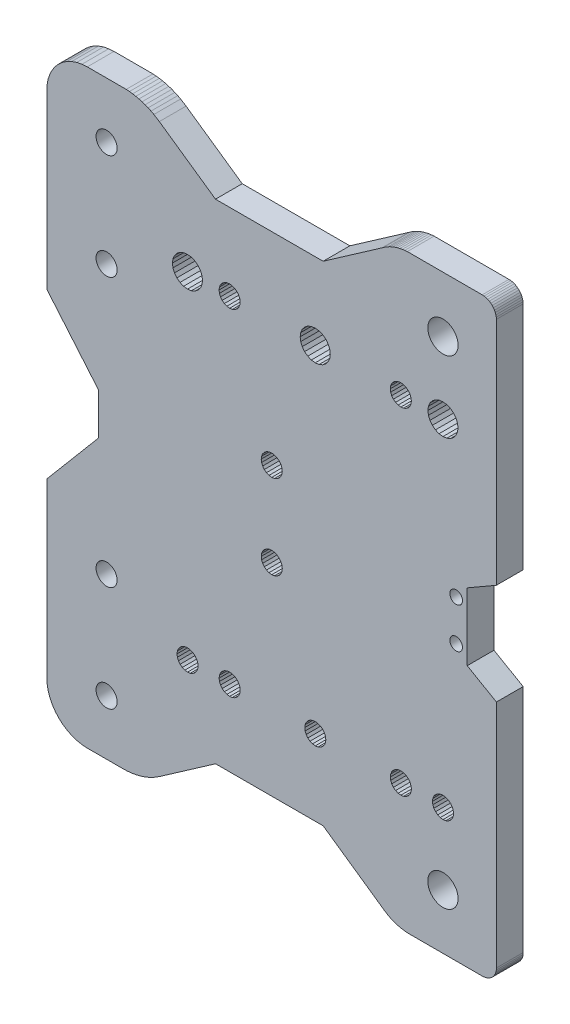
SolidWorks part; units mm, degrees
ref_plane "Front Plane" through (0, 0, 0) normal (0, 0, 1) x (1, 0, 0)
ref_plane "Top Plane" through (0, 0, 0) normal (0, 1, 0) x (1, 0, 0)
ref_plane "Right Plane" through (0, 0, 0) normal (1, 0, 0) x (0, 0, -1)
sketch "Model" plane through (0, 0, 0) normal (0, 0, 1) x (1, 0, 0)
  line L0 (606.5044, 163.4555) -> (606.5078, 147.4555)
  line L1 (516.3162, 225.4614) -> (516.3365, 85.4197) construction
  line L2 (516.3264, 155.4406) -> (606.5061, 155.4555) construction
  line L3 (600.743, 195.2513) -> (600.743, 115.4517) construction
  line L4 (606.5078, 147.4555) -> (613.436, 143.4555)
  line L5 (613.4326, 167.4555) -> (606.5044, 163.4555)
  line L8 (606.5078, 151.9787) -> (606.5068, 151.9792)
  line L12 (547.9387, 193.9942) -> (548.336, 193.4765)
  line L13 (557.9459, 144.2266) -> (558.3432, 143.7089)
  line L14 (598.5902, 114.201) -> (598.9876, 113.6833)
  line L15 (597.6529, 197.0356) -> (597.2965, 196.1749)
  line L16 (537.9502, 114.1922) -> (538.3476, 113.6745)
  line L17 (547.9502, 114.2067) -> (548.3476, 113.689)
  line L18 (567.3374, 197.0312) -> (566.9811, 196.1705)
  line L19 (568.2747, 114.1966) -> (568.6721, 113.6789)
  line L21 (588.5902, 114.2126) -> (588.9876, 113.6949)
  line L23 (588.5787, 194) -> (588.976, 193.4823)
  line L24 (557.943, 164.2266) -> (558.3403, 163.7089)
  line L25 (537.0129, 197.0268) -> (536.6565, 196.1661)
  line L28 (612.7493, 86.751) -> (612.4593, 86.4203)
  line L52 (548.336, 193.4765) -> (548.8539, 193.0792)
  line L53 (548.8539, 193.0792) -> (549.4569, 192.8296)
  line L54 (549.4569, 192.8296) -> (550.1039, 192.7445)
  line L55 (550.1039, 192.7445) -> (550.7509, 192.8298)
  line L56 (550.7509, 192.8298) -> (551.3539, 193.0796)
  line L57 (551.3539, 193.0796) -> (551.8716, 193.477)
  line L58 (551.8716, 193.477) -> (552.2688, 193.9948)
  line L59 (552.2688, 193.9948) -> (552.5185, 194.5978)
  line L60 (552.5185, 194.5978) -> (552.6036, 195.2448)
  line L61 (552.6036, 195.2448) -> (552.5183, 195.8919)
  line L62 (552.5183, 195.8919) -> (552.2684, 196.4948)
  line L63 (552.2684, 196.4948) -> (551.8711, 197.0125)
  line L64 (551.8711, 197.0125) -> (551.3532, 197.4097)
  line L65 (551.3532, 197.4097) -> (550.7503, 197.6594)
  line L66 (550.7503, 197.6594) -> (550.1032, 197.7445)
  line L67 (550.1032, 197.7445) -> (549.4562, 197.6592)
  line L68 (549.4562, 197.6592) -> (548.8532, 197.4094)
  line L69 (548.8532, 197.4094) -> (548.3355, 197.012)
  line L70 (548.3355, 197.012) -> (547.9383, 196.4942)
  line L71 (547.9383, 196.4942) -> (547.6886, 195.8912)
  line L72 (547.6886, 195.8912) -> (547.6036, 195.2441)
  line L73 (547.6036, 195.2441) -> (547.6888, 194.5971)
  line L74 (547.6888, 194.5971) -> (547.9387, 193.9942)
  line L75 (558.3432, 143.7089) -> (558.8611, 143.3117)
  line L76 (558.8611, 143.3117) -> (559.464, 143.062)
  line L77 (559.464, 143.062) -> (560.1111, 142.9769)
  line L78 (560.1111, 142.9769) -> (560.7581, 143.0622)
  line L79 (560.7581, 143.0622) -> (561.3611, 143.312)
  line L80 (561.3611, 143.312) -> (561.8788, 143.7094)
  line L81 (561.8788, 143.7094) -> (562.276, 144.2272)
  line L82 (562.276, 144.2272) -> (562.5256, 144.8302)
  line L83 (562.5256, 144.8302) -> (562.6107, 145.4773)
  line L84 (562.6107, 145.4773) -> (562.5255, 146.1243)
  line L85 (562.5255, 146.1243) -> (562.2756, 146.7272)
  line L86 (562.2756, 146.7272) -> (561.8783, 147.2449)
  line L87 (561.8783, 147.2449) -> (561.3604, 147.6422)
  line L88 (561.3604, 147.6422) -> (560.7574, 147.8918)
  line L89 (560.7574, 147.8918) -> (560.1104, 147.9769)
  line L90 (560.1104, 147.9769) -> (559.4633, 147.8916)
  line L91 (559.4633, 147.8916) -> (558.8604, 147.6418)
  line L92 (558.8604, 147.6418) -> (558.3427, 147.2444)
  line L93 (558.3427, 147.2444) -> (557.9455, 146.7266)
  line L94 (557.9455, 146.7266) -> (557.6958, 146.1236)
  line L95 (557.6958, 146.1236) -> (557.6107, 145.4766)
  line L96 (557.6107, 145.4766) -> (557.696, 144.8295)
  line L97 (557.696, 144.8295) -> (557.9459, 144.2266)
  line L98 (598.9876, 113.6833) -> (599.5054, 113.2861)
  line L99 (599.5054, 113.2861) -> (600.1084, 113.0364)
  line L100 (600.1084, 113.0364) -> (600.7554, 112.9513)
  line L101 (600.7554, 112.9513) -> (601.4025, 113.0366)
  line L102 (601.4025, 113.0366) -> (602.0054, 113.2864)
  line L103 (602.0054, 113.2864) -> (602.5231, 113.6838)
  line L104 (602.5231, 113.6838) -> (602.9203, 114.2016)
  line L105 (602.9203, 114.2016) -> (603.17, 114.8046)
  line L106 (603.17, 114.8046) -> (603.2551, 115.4517)
  line L107 (603.2551, 115.4517) -> (603.1698, 116.0987)
  line L108 (603.1698, 116.0987) -> (602.92, 116.7016)
  line L109 (602.92, 116.7016) -> (602.5226, 117.2193)
  line L110 (602.5226, 117.2193) -> (602.0048, 117.6166)
  line L111 (602.0048, 117.6166) -> (601.4018, 117.8662)
  line L112 (601.4018, 117.8662) -> (600.7547, 117.9513)
  line L113 (600.7547, 117.9513) -> (600.1077, 117.866)
  line L114 (600.1077, 117.866) -> (599.5048, 117.6162)
  line L115 (599.5048, 117.6162) -> (598.9871, 117.2188)
  line L116 (598.9871, 117.2188) -> (598.5898, 116.701)
  line L117 (598.5898, 116.701) -> (598.3402, 116.098)
  line L118 (598.3402, 116.098) -> (598.2551, 115.4509)
  line L119 (598.2551, 115.4509) -> (598.3404, 114.8039)
  line L120 (598.3404, 114.8039) -> (598.5902, 114.201)
  line L121 (597.2965, 196.1749) -> (597.1751, 195.2513)
  line L122 (597.1751, 195.2513) -> (597.2968, 194.3277)
  line L123 (597.2968, 194.3277) -> (597.6534, 193.4671)
  line L124 (597.6534, 193.4671) -> (598.2206, 192.7281)
  line L125 (598.2206, 192.7281) -> (598.9597, 192.1611)
  line L126 (598.9597, 192.1611) -> (599.8205, 191.8048)
  line L127 (599.8205, 191.8048) -> (600.7441, 191.6833)
  line L128 (600.7441, 191.6833) -> (601.6676, 191.805)
  line L129 (601.6676, 191.805) -> (602.5282, 192.1616)
  line L130 (602.5282, 192.1616) -> (603.2672, 192.7288)
  line L131 (603.2672, 192.7288) -> (603.8342, 193.468)
  line L132 (603.8342, 193.468) -> (604.1906, 194.3287)
  line L133 (604.1906, 194.3287) -> (604.3121, 195.2523)
  line L134 (604.3121, 195.2523) -> (604.1903, 196.1759)
  line L135 (604.1903, 196.1759) -> (603.8337, 197.0365)
  line L136 (603.8337, 197.0365) -> (603.2665, 197.7755)
  line L137 (603.2665, 197.7755) -> (602.5274, 198.3425)
  line L138 (602.5274, 198.3425) -> (601.6666, 198.6988)
  line L139 (601.6666, 198.6988) -> (600.743, 198.8203)
  line L140 (600.743, 198.8203) -> (599.8195, 198.6986)
  line L141 (599.8195, 198.6986) -> (598.9589, 198.3419)
  line L142 (598.9589, 198.3419) -> (598.2199, 197.7747)
  line L143 (598.2199, 197.7747) -> (597.6529, 197.0356)
  line L144 (538.3476, 113.6745) -> (538.8654, 113.2773)
  line L145 (538.8654, 113.2773) -> (539.4684, 113.0276)
  line L146 (539.4684, 113.0276) -> (540.1154, 112.9425)
  line L147 (540.1154, 112.9425) -> (540.7625, 113.0278)
  line L148 (540.7625, 113.0278) -> (541.3654, 113.2777)
  line L149 (541.3654, 113.2777) -> (541.8831, 113.675)
  line L150 (541.8831, 113.675) -> (542.2803, 114.1929)
  line L151 (542.2803, 114.1929) -> (542.53, 114.7959)
  line L152 (542.53, 114.7959) -> (542.6151, 115.4429)
  line L153 (542.6151, 115.4429) -> (542.5298, 116.0899)
  line L154 (542.5298, 116.0899) -> (542.28, 116.6929)
  line L155 (542.28, 116.6929) -> (541.8826, 117.2106)
  line L156 (541.8826, 117.2106) -> (541.3648, 117.6078)
  line L157 (541.3648, 117.6078) -> (540.7618, 117.8575)
  line L158 (540.7618, 117.8575) -> (540.1147, 117.9425)
  line L159 (540.1147, 117.9425) -> (539.4677, 117.8573)
  line L160 (539.4677, 117.8573) -> (538.8648, 117.6074)
  line L161 (538.8648, 117.6074) -> (538.3471, 117.2101)
  line L162 (538.3471, 117.2101) -> (537.9498, 116.6922)
  line L163 (537.9498, 116.6922) -> (537.7002, 116.0892)
  line L164 (537.7002, 116.0892) -> (537.6151, 115.4422)
  line L165 (537.6151, 115.4422) -> (537.7004, 114.7952)
  line L166 (537.7004, 114.7952) -> (537.9502, 114.1922)
  line L167 (548.3476, 113.689) -> (548.8654, 113.2918)
  line L168 (548.8654, 113.2918) -> (549.4684, 113.0421)
  line L169 (549.4684, 113.0421) -> (550.1154, 112.957)
  line L170 (550.1154, 112.957) -> (550.7625, 113.0423)
  line L171 (550.7625, 113.0423) -> (551.3654, 113.2921)
  line L172 (551.3654, 113.2921) -> (551.8831, 113.6895)
  line L173 (551.8831, 113.6895) -> (552.2803, 114.2073)
  line L174 (552.2803, 114.2073) -> (552.53, 114.8103)
  line L175 (552.53, 114.8103) -> (552.6151, 115.4574)
  line L176 (552.6151, 115.4574) -> (552.5298, 116.1044)
  line L177 (552.5298, 116.1044) -> (552.28, 116.7073)
  line L178 (552.28, 116.7073) -> (551.8826, 117.225)
  line L179 (551.8826, 117.225) -> (551.3648, 117.6223)
  line L180 (551.3648, 117.6223) -> (550.7618, 117.8719)
  line L181 (550.7618, 117.8719) -> (550.1147, 117.957)
  line L182 (550.1147, 117.957) -> (549.4677, 117.8717)
  line L183 (549.4677, 117.8717) -> (548.8648, 117.6219)
  line L184 (548.8648, 117.6219) -> (548.3471, 117.2245)
  line L185 (548.3471, 117.2245) -> (547.9498, 116.7067)
  line L186 (547.9498, 116.7067) -> (547.7002, 116.1037)
  line L187 (547.7002, 116.1037) -> (547.6151, 115.4567)
  line L188 (547.6151, 115.4567) -> (547.7004, 114.8096)
  line L189 (547.7004, 114.8096) -> (547.9502, 114.2067)
  line L190 (566.9811, 196.1705) -> (566.8596, 195.2469)
  line L191 (566.8596, 195.2469) -> (566.9813, 194.3233)
  line L192 (566.9813, 194.3233) -> (567.3379, 193.4627)
  line L193 (567.3379, 193.4627) -> (567.9051, 192.7237)
  line L194 (567.9051, 192.7237) -> (568.6443, 192.1567)
  line L195 (568.6443, 192.1567) -> (569.505, 191.8004)
  line L196 (569.505, 191.8004) -> (570.4286, 191.6789)
  line L197 (570.4286, 191.6789) -> (571.3522, 191.8006)
  line L198 (571.3522, 191.8006) -> (572.2128, 192.1573)
  line L199 (572.2128, 192.1573) -> (572.9518, 192.7245)
  line L200 (572.9518, 192.7245) -> (573.5188, 193.4636)
  line L201 (573.5188, 193.4636) -> (573.8751, 194.3243)
  line L202 (573.8751, 194.3243) -> (573.9966, 195.2479)
  line L203 (573.9966, 195.2479) -> (573.8749, 196.1715)
  line L204 (573.8749, 196.1715) -> (573.5182, 197.0321)
  line L205 (573.5182, 197.0321) -> (572.951, 197.7711)
  line L206 (572.951, 197.7711) -> (572.2119, 198.3381)
  line L207 (572.2119, 198.3381) -> (571.3512, 198.6945)
  line L208 (571.3512, 198.6945) -> (570.4276, 198.8159)
  line L209 (570.4276, 198.8159) -> (569.504, 198.6942)
  line L210 (569.504, 198.6942) -> (568.6434, 198.3376)
  line L211 (568.6434, 198.3376) -> (567.9044, 197.7704)
  line L212 (567.9044, 197.7704) -> (567.3374, 197.0312)
  line L213 (568.6721, 113.6789) -> (569.1899, 113.2817)
  line L214 (569.1899, 113.2817) -> (569.7929, 113.032)
  line L215 (569.7929, 113.032) -> (570.44, 112.9469)
  line L216 (570.44, 112.9469) -> (571.087, 113.0322)
  line L217 (571.087, 113.0322) -> (571.6899, 113.282)
  line L218 (571.6899, 113.282) -> (572.2076, 113.6794)
  line L219 (572.2076, 113.6794) -> (572.6049, 114.1972)
  line L220 (572.6049, 114.1972) -> (572.8545, 114.8002)
  line L221 (572.8545, 114.8002) -> (572.9396, 115.4473)
  line L222 (572.9396, 115.4473) -> (572.8543, 116.0943)
  line L223 (572.8543, 116.0943) -> (572.6045, 116.6972)
  line L224 (572.6045, 116.6972) -> (572.2071, 117.215)
  line L225 (572.2071, 117.215) -> (571.6893, 117.6122)
  line L226 (571.6893, 117.6122) -> (571.0863, 117.8618)
  line L227 (571.0863, 117.8618) -> (570.4393, 117.9469)
  line L228 (570.4393, 117.9469) -> (569.7922, 117.8617)
  line L229 (569.7922, 117.8617) -> (569.1893, 117.6118)
  line L230 (569.1893, 117.6118) -> (568.6716, 117.2144)
  line L231 (568.6716, 117.2144) -> (568.2744, 116.6966)
  line L232 (568.2744, 116.6966) -> (568.0247, 116.0936)
  line L233 (568.0247, 116.0936) -> (567.9396, 115.4466)
  line L234 (567.9396, 115.4466) -> (568.0249, 114.7995)
  line L235 (568.0249, 114.7995) -> (568.2747, 114.1966)
  line L259 (588.9876, 113.6949) -> (589.5054, 113.2976)
  line L260 (589.5054, 113.2976) -> (590.1084, 113.048)
  line L261 (590.1084, 113.048) -> (590.7554, 112.9629)
  line L262 (590.7554, 112.9629) -> (591.4025, 113.0482)
  line L263 (591.4025, 113.0482) -> (592.0054, 113.298)
  line L264 (592.0054, 113.298) -> (592.5231, 113.6954)
  line L265 (592.5231, 113.6954) -> (592.9203, 114.2132)
  line L266 (592.9203, 114.2132) -> (593.17, 114.8162)
  line L267 (593.17, 114.8162) -> (593.2551, 115.4632)
  line L268 (593.2551, 115.4632) -> (593.1698, 116.1103)
  line L269 (593.1698, 116.1103) -> (592.92, 116.7132)
  line L270 (592.92, 116.7132) -> (592.5226, 117.2309)
  line L271 (592.5226, 117.2309) -> (592.0048, 117.6281)
  line L272 (592.0048, 117.6281) -> (591.4018, 117.8778)
  line L273 (591.4018, 117.8778) -> (590.7547, 117.9629)
  line L274 (590.7547, 117.9629) -> (590.1077, 117.8776)
  line L275 (590.1077, 117.8776) -> (589.5048, 117.6278)
  line L276 (589.5048, 117.6278) -> (588.9871, 117.2304)
  line L277 (588.9871, 117.2304) -> (588.5898, 116.7126)
  line L278 (588.5898, 116.7126) -> (588.3402, 116.1096)
  line L279 (588.3402, 116.1096) -> (588.2551, 115.4625)
  line L280 (588.2551, 115.4625) -> (588.3404, 114.8155)
  line L281 (588.3404, 114.8155) -> (588.5902, 114.2126)
  line L305 (588.976, 193.4823) -> (589.4939, 193.0851)
  line L306 (589.4939, 193.0851) -> (590.0969, 192.8354)
  line L307 (590.0969, 192.8354) -> (590.7439, 192.7503)
  line L308 (590.7439, 192.7503) -> (591.3909, 192.8356)
  line L309 (591.3909, 192.8356) -> (591.9939, 193.0855)
  line L310 (591.9939, 193.0855) -> (592.5116, 193.4828)
  line L311 (592.5116, 193.4828) -> (592.9088, 194.0007)
  line L312 (592.9088, 194.0007) -> (593.1585, 194.6036)
  line L313 (593.1585, 194.6036) -> (593.2436, 195.2507)
  line L314 (593.2436, 195.2507) -> (593.1583, 195.8977)
  line L315 (593.1583, 195.8977) -> (592.9084, 196.5007)
  line L316 (592.9084, 196.5007) -> (592.5111, 197.0184)
  line L317 (592.5111, 197.0184) -> (591.9932, 197.4156)
  line L318 (591.9932, 197.4156) -> (591.3903, 197.6653)
  line L319 (591.3903, 197.6653) -> (590.7432, 197.7503)
  line L320 (590.7432, 197.7503) -> (590.0962, 197.6651)
  line L321 (590.0962, 197.6651) -> (589.4932, 197.4152)
  line L322 (589.4932, 197.4152) -> (588.9755, 197.0179)
  line L323 (588.9755, 197.0179) -> (588.5783, 196.5)
  line L324 (588.5783, 196.5) -> (588.3286, 195.897)
  line L325 (588.3286, 195.897) -> (588.2436, 195.25)
  line L326 (588.2436, 195.25) -> (588.3288, 194.603)
  line L327 (588.3288, 194.603) -> (588.5787, 194)
  line L328 (558.3403, 163.7089) -> (558.8582, 163.3117)
  line L329 (558.8582, 163.3117) -> (559.4612, 163.062)
  line L330 (559.4612, 163.062) -> (560.1082, 162.9769)
  line L331 (560.1082, 162.9769) -> (560.7552, 163.0622)
  line L332 (560.7552, 163.0622) -> (561.3582, 163.312)
  line L333 (561.3582, 163.312) -> (561.8759, 163.7094)
  line L334 (561.8759, 163.7094) -> (562.2731, 164.2272)
  line L335 (562.2731, 164.2272) -> (562.5228, 164.8302)
  line L336 (562.5228, 164.8302) -> (562.6079, 165.4773)
  line L337 (562.6079, 165.4773) -> (562.5226, 166.1243)
  line L338 (562.5226, 166.1243) -> (562.2727, 166.7272)
  line L339 (562.2727, 166.7272) -> (561.8754, 167.2449)
  line L340 (561.8754, 167.2449) -> (561.3575, 167.6422)
  line L341 (561.3575, 167.6422) -> (560.7546, 167.8918)
  line L342 (560.7546, 167.8918) -> (560.1075, 167.9769)
  line L343 (560.1075, 167.9769) -> (559.4605, 167.8916)
  line L344 (559.4605, 167.8916) -> (558.8575, 167.6418)
  line L345 (558.8575, 167.6418) -> (558.3398, 167.2444)
  line L346 (558.3398, 167.2444) -> (557.9426, 166.7266)
  line L347 (557.9426, 166.7266) -> (557.6929, 166.1236)
  line L348 (557.6929, 166.1236) -> (557.6079, 165.4766)
  line L349 (557.6079, 165.4766) -> (557.6931, 164.8295)
  line L350 (557.6931, 164.8295) -> (557.943, 164.2266)
  line L351 (536.6565, 196.1661) -> (536.5351, 195.2425)
  line L352 (536.5351, 195.2425) -> (536.6568, 194.3189)
  line L353 (536.6568, 194.3189) -> (537.0134, 193.4583)
  line L354 (537.0134, 193.4583) -> (537.5806, 192.7194)
  line L355 (537.5806, 192.7194) -> (538.3197, 192.1524)
  line L356 (538.3197, 192.1524) -> (539.1805, 191.796)
  line L357 (539.1805, 191.796) -> (540.1041, 191.6745)
  line L358 (540.1041, 191.6745) -> (541.0276, 191.7963)
  line L359 (541.0276, 191.7963) -> (541.8882, 192.1529)
  line L360 (541.8882, 192.1529) -> (542.6272, 192.7201)
  line L361 (542.6272, 192.7201) -> (543.1942, 193.4592)
  line L362 (543.1942, 193.4592) -> (543.5506, 194.3199)
  line L363 (543.5506, 194.3199) -> (543.6721, 195.2435)
  line L364 (543.6721, 195.2435) -> (543.5503, 196.1671)
  line L365 (543.5503, 196.1671) -> (543.1937, 197.0277)
  line L366 (543.1937, 197.0277) -> (542.6265, 197.7667)
  line L367 (542.6265, 197.7667) -> (541.8874, 198.3337)
  line L368 (541.8874, 198.3337) -> (541.0266, 198.6901)
  line L369 (541.0266, 198.6901) -> (540.103, 198.8115)
  line L370 (540.103, 198.8115) -> (539.1795, 198.6898)
  line L371 (539.1795, 198.6898) -> (538.3189, 198.3332)
  line L372 (538.3189, 198.3332) -> (537.5799, 197.766)
  line L373 (537.5799, 197.766) -> (537.0129, 197.0268)
  line L420 (612.4593, 86.4203) -> (612.1287, 86.1302)
  line L421 (612.1287, 86.1302) -> (611.763, 85.8857)
  line L422 (611.763, 85.8857) -> (611.3685, 85.6911)
  line L423 (611.3685, 85.6911) -> (610.952, 85.5497)
  line L424 (610.952, 85.5497) -> (610.5206, 85.4638)
  line L425 (610.5206, 85.4638) -> (610.0816, 85.435)
  line L426 (610.0816, 85.435) -> (592.9058, 85.4393)
  line L427 (592.9058, 85.4393) -> (592.3094, 85.4556)
  line L428 (592.3094, 85.4556) -> (591.7149, 85.5048)
  line L429 (591.7149, 85.5048) -> (591.1241, 85.5868)
  line L430 (591.1241, 85.5868) -> (590.5386, 85.7013)
  line L431 (590.5386, 85.7013) -> (589.9604, 85.8479)
  line L432 (589.9604, 85.8479) -> (589.3911, 86.0262)
  line L433 (589.3911, 86.0262) -> (588.8325, 86.2356)
  line L434 (588.8325, 86.2356) -> (588.2864, 86.4756)
  line L435 (588.2864, 86.4756) -> (587.7543, 86.7454)
  line L436 (587.7543, 86.7454) -> (586.7389, 87.3709)
  line L437 (586.7389, 87.3709) -> (586.2586, 87.7247)
  line L438 (586.2586, 87.7247) -> (572.3183, 97.4366)
  line L439 (572.3183, 97.4366) -> (546.771, 97.4246)
  line L440 (546.771, 97.4246) -> (533.438, 88.1304)
  line L441 (533.438, 88.1304) -> (532.1409, 87.3207)
  line L442 (532.1409, 87.3207) -> (531.4632, 86.9662)
  line L443 (531.4632, 86.9662) -> (530.7685, 86.6465)
  line L444 (530.7685, 86.6465) -> (530.0584, 86.3624)
  line L445 (530.0584, 86.3624) -> (529.3348, 86.1147)
  line L446 (529.3348, 86.1147) -> (528.5996, 85.904)
  line L447 (528.5996, 85.904) -> (527.8547, 85.7309)
  line L448 (527.8547, 85.7309) -> (527.1019, 85.5957)
  line L449 (527.1019, 85.5957) -> (526.3433, 85.4989)
  line L450 (526.3433, 85.4989) -> (525.5807, 85.4406)
  line L451 (525.5807, 85.4406) -> (524.8162, 85.4211)
  line L452 (524.8162, 85.4211) -> (516.3365, 85.4197)
  line L453 (516.3365, 85.4197) -> (515.0824, 85.5018)
  line L454 (515.0824, 85.5018) -> (513.8497, 85.7468)
  line L455 (513.8497, 85.7468) -> (512.6595, 86.1506)
  line L456 (512.6595, 86.1506) -> (511.5323, 86.7063)
  line L457 (511.5323, 86.7063) -> (510.4872, 87.4044)
  line L458 (510.4872, 87.4044) -> (509.5422, 88.2329)
  line L459 (509.5422, 88.2329) -> (508.7134, 89.1777)
  line L460 (508.7134, 89.1777) -> (508.015, 90.2225)
  line L461 (508.015, 90.2225) -> (507.4589, 91.3496)
  line L462 (507.4589, 91.3496) -> (507.0548, 92.5397)
  line L463 (507.0548, 92.5397) -> (506.8094, 93.7723)
  line L464 (506.8094, 93.7723) -> (506.727, 95.0264)
  line L465 (506.727, 95.0264) -> (506.7211, 135.9628)
  line L466 (506.7211, 135.9628) -> (518.9364, 150.4418)
  line L467 (518.9364, 150.4418) -> (518.935, 160.4418)
  line L468 (518.935, 160.4418) -> (506.7155, 174.9444)
  line L469 (506.7155, 174.9444) -> (506.7096, 215.852)
  line L470 (506.7096, 215.852) -> (506.7916, 217.1061)
  line L471 (506.7916, 217.1061) -> (507.0366, 218.3388)
  line L472 (507.0366, 218.3388) -> (507.4404, 219.529)
  line L473 (507.4404, 219.529) -> (507.9961, 220.6562)
  line L474 (507.9961, 220.6562) -> (508.6942, 221.7013)
  line L475 (508.6942, 221.7013) -> (509.5227, 222.6463)
  line L476 (509.5227, 222.6463) -> (510.4675, 223.4751)
  line L477 (510.4675, 223.4751) -> (511.5124, 224.1735)
  line L478 (511.5124, 224.1735) -> (512.6395, 224.7295)
  line L479 (512.6395, 224.7295) -> (513.8295, 225.1337)
  line L480 (513.8295, 225.1337) -> (515.0621, 225.3791)
  line L481 (515.0621, 225.3791) -> (516.3162, 225.4614)
  line L482 (516.3162, 225.4614) -> (525.5605, 225.4615)
  line L483 (525.5605, 225.4615) -> (526.3231, 225.4035)
  line L484 (526.3231, 225.4035) -> (527.0818, 225.3069)
  line L485 (527.0818, 225.3069) -> (527.8345, 225.1719)
  line L486 (527.8345, 225.1719) -> (528.5795, 224.999)
  line L487 (528.5795, 224.999) -> (529.3148, 224.7885)
  line L488 (529.3148, 224.7885) -> (530.0384, 224.541)
  line L489 (530.0384, 224.541) -> (530.7486, 224.2571)
  line L490 (530.7486, 224.2571) -> (531.4435, 223.9376)
  line L491 (531.4435, 223.9376) -> (532.1212, 223.5833)
  line L492 (532.1212, 223.5833) -> (533.4186, 222.774)
  line L493 (533.4186, 222.774) -> (546.7543, 213.4837)
  line L494 (546.7543, 213.4837) -> (572.3016, 213.4949)
  line L495 (572.3016, 213.4949) -> (586.239, 223.2107)
  line L496 (586.239, 223.2107) -> (586.7192, 223.5647)
  line L497 (586.7192, 223.5647) -> (587.7345, 224.1905)
  line L498 (587.7345, 224.1905) -> (588.2665, 224.4604)
  line L499 (588.2665, 224.4604) -> (588.8125, 224.7006)
  line L500 (588.8125, 224.7006) -> (589.371, 224.9102)
  line L501 (589.371, 224.9102) -> (589.9402, 225.0887)
  line L502 (589.9402, 225.0887) -> (590.5184, 225.2354)
  line L503 (590.5184, 225.2354) -> (591.1039, 225.3501)
  line L504 (591.1039, 225.3501) -> (591.6947, 225.4322)
  line L505 (591.6947, 225.4322) -> (592.2892, 225.4816)
  line L506 (592.2892, 225.4816) -> (610.0614, 225.475)
  line L507 (610.0614, 225.475) -> (610.5003, 225.4463)
  line L508 (610.5003, 225.4463) -> (610.9318, 225.3605)
  line L509 (610.9318, 225.3605) -> (611.3483, 225.2192)
  line L510 (611.3483, 225.2192) -> (611.7429, 225.0247)
  line L511 (611.7429, 225.0247) -> (612.1086, 224.7804)
  line L512 (612.1086, 224.7804) -> (612.4394, 224.4904)
  line L513 (612.4394, 224.4904) -> (612.7295, 224.1597)
  line L514 (612.7295, 224.1597) -> (612.9739, 223.794)
  line L515 (612.9739, 223.794) -> (613.1685, 223.3995)
  line L516 (613.1685, 223.3995) -> (613.31, 222.983)
  line L517 (613.31, 222.983) -> (613.3958, 222.5516)
  line L518 (613.3958, 222.5516) -> (613.4247, 222.1127)
  line L519 (613.4247, 222.1127) -> (613.4326, 167.4555)
  line L520 (613.4439, 88.7982) -> (613.4152, 88.3593)
  line L521 (613.4152, 88.3593) -> (613.3295, 87.9279)
  line L522 (613.3295, 87.9279) -> (613.1881, 87.5113)
  line L523 (613.1881, 87.5113) -> (612.9936, 87.1168)
  line L524 (612.9936, 87.1168) -> (612.7493, 86.751)
  line L548 (613.436, 143.4555) -> (613.4439, 88.7982)
  circle A0 centre (520.9018, 187.2428) radius 2.5
  circle A1 centre (603.8813, 150.6644) radius 1.5
  circle A2 centre (603.8813, 160.2444) radius 1.5
  circle A3 centre (520.9023, 123.4766) radius 2.5
  circle A4 centre (600.7425, 98.4796) radius 3.6
  circle A5 centre (600.7453, 212.2458) radius 3.6
  arc A6 (604.8324, 161.4042) -> (604.8324, 159.0845) centre (603.8813, 160.2444) ccw
  circle A7 centre (520.9053, 212.2458) radius 2.5
  circle A8 centre (520.9061, 98.4796) radius 2.5
  point P6 (0, 0)
extrude "Boss-Extrude1" add sketch "Model" along normal blind 6.35
